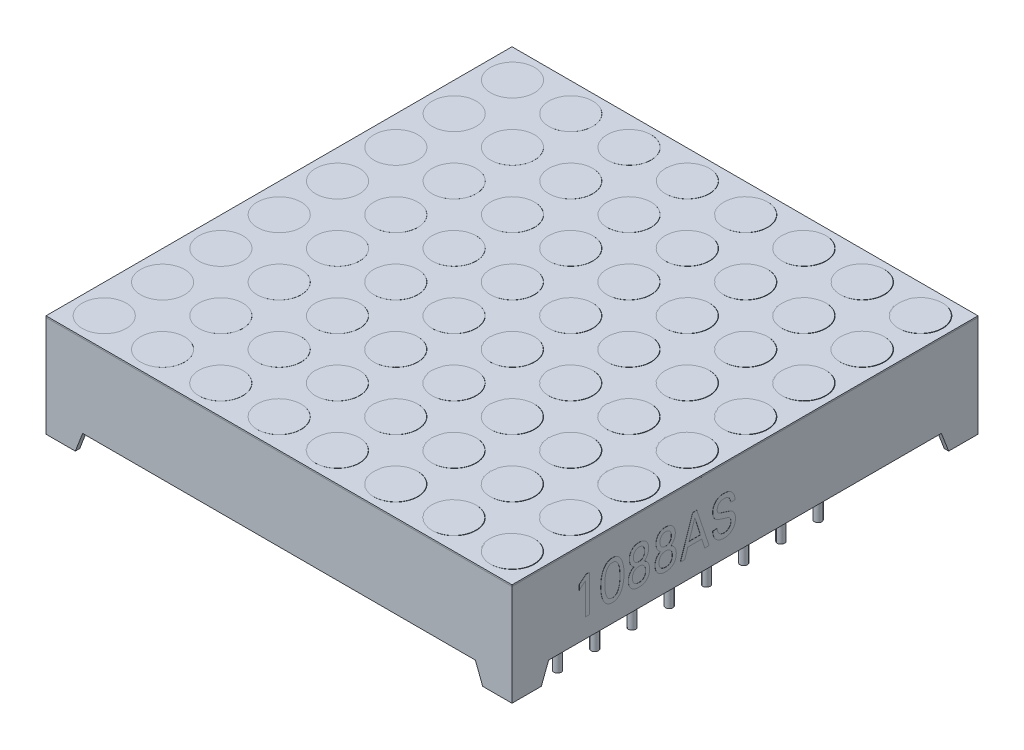
SolidWorks part; units mm, degrees
ref_plane "Front Plane" through (0, 0, 0) normal (0, 0, 1) x (1, 0, 0)
ref_plane "Top Plane" through (0, 0, 0) normal (0, 1, 0) x (1, 0, 0)
ref_plane "Right Plane" through (0, 0, 0) normal (1, 0, 0) x (0, 0, -1)
sketch "Sketch1" plane through (0, 0, 0) normal (0, 1, 0) x (1, 0, 0)
  line L0 (3.975, 31.8) -> (3.975, 0) construction
  line L1 (0, 0) -> (31.8, 0)
  line L2 (0, 0) -> (0, 31.8)
  line L3 (0, 31.8) -> (31.8, 31.8)
  line L4 (31.8, 0) -> (31.8, 31.8)
  line L5 (7.955, 31.8) -> (7.955, 0) construction
  line L6 (11.935, 31.8) -> (11.935, 0) construction
  line L7 (15.915, 31.8) -> (15.915, 0) construction
  line L8 (19.895, 31.8) -> (19.895, 0) construction
  line L9 (23.875, 31.8) -> (23.875, 0) construction
  line L10 (27.855, 31.8) -> (27.855, 0) construction
  line L11 (0, 3.975) -> (31.8, 3.975) construction
  line L12 (0, 7.955) -> (31.8, 7.955) construction
  line L13 (0, 11.935) -> (31.8, 11.935) construction
  line L14 (0, 15.915) -> (31.8, 15.915) construction
  line L15 (0, 19.895) -> (31.8, 19.895) construction
  line L16 (0, 23.875) -> (31.8, 23.875) construction
  line L17 (0, 27.855) -> (31.8, 27.855) construction
  line L18 (0, 0) -> (3.975, 3.975) construction
  line L19 (0, 3.975) -> (3.975, 0) construction
  circle A0 centre (1.9875, 1.9875) radius 1.5
  circle A1 centre (5.9675, 1.9875) radius 1.5
  circle A2 centre (9.9475, 1.9875) radius 1.5
  circle A3 centre (13.9275, 1.9875) radius 1.5
  circle A4 centre (17.9075, 1.9875) radius 1.5
  circle A5 centre (21.8875, 1.9875) radius 1.5
  circle A6 centre (25.8675, 1.9875) radius 1.5
  circle A7 centre (29.8475, 1.9875) radius 1.5
  circle A8 centre (5.9675, 5.9675) radius 1.5
  circle A9 centre (9.9475, 5.9675) radius 1.5
  circle A10 centre (13.9275, 5.9675) radius 1.5
  circle A11 centre (17.9075, 5.9675) radius 1.5
  circle A12 centre (21.8875, 5.9675) radius 1.5
  circle A13 centre (25.8675, 5.9675) radius 1.5
  circle A14 centre (29.8475, 5.9675) radius 1.5
  circle A15 centre (5.9675, 9.9475) radius 1.5
  circle A16 centre (9.9475, 9.9475) radius 1.5
  circle A17 centre (13.9275, 9.9475) radius 1.5
  circle A18 centre (17.9075, 9.9475) radius 1.5
  circle A19 centre (21.8875, 9.9475) radius 1.5
  circle A20 centre (25.8675, 9.9475) radius 1.5
  circle A21 centre (29.8475, 9.9475) radius 1.5
  circle A22 centre (5.9675, 13.9275) radius 1.5
  circle A23 centre (9.9475, 13.9275) radius 1.5
  circle A24 centre (13.9275, 13.9275) radius 1.5
  circle A25 centre (17.9075, 13.9275) radius 1.5
  circle A26 centre (21.8875, 13.9275) radius 1.5
  circle A27 centre (25.8675, 13.9275) radius 1.5
  circle A28 centre (29.8475, 13.9275) radius 1.5
  circle A29 centre (5.9675, 17.9075) radius 1.5
  circle A30 centre (9.9475, 17.9075) radius 1.5
  circle A31 centre (13.9275, 17.9075) radius 1.5
  circle A32 centre (17.9075, 17.9075) radius 1.5
  circle A33 centre (21.8875, 17.9075) radius 1.5
  circle A34 centre (25.8675, 17.9075) radius 1.5
  circle A35 centre (29.8475, 17.9075) radius 1.5
  circle A36 centre (5.9675, 21.8875) radius 1.5
  circle A37 centre (9.9475, 21.8875) radius 1.5
  circle A38 centre (13.9275, 21.8875) radius 1.5
  circle A39 centre (17.9075, 21.8875) radius 1.5
  circle A40 centre (21.8875, 21.8875) radius 1.5
  circle A41 centre (25.8675, 21.8875) radius 1.5
  circle A42 centre (29.8475, 21.8875) radius 1.5
  circle A43 centre (5.9675, 25.8675) radius 1.5
  circle A44 centre (9.9475, 25.8675) radius 1.5
  circle A45 centre (13.9275, 25.8675) radius 1.5
  circle A46 centre (17.9075, 25.8675) radius 1.5
  circle A47 centre (21.8875, 25.8675) radius 1.5
  circle A48 centre (25.8675, 25.8675) radius 1.5
  circle A49 centre (29.8475, 25.8675) radius 1.5
  circle A50 centre (5.9675, 29.8475) radius 1.5
  circle A51 centre (9.9475, 29.8475) radius 1.5
  circle A52 centre (13.9275, 29.8475) radius 1.5
  circle A53 centre (17.9075, 29.8475) radius 1.5
  circle A54 centre (21.8875, 29.8475) radius 1.5
  circle A55 centre (25.8675, 29.8475) radius 1.5
  circle A56 centre (29.8475, 29.8475) radius 1.5
  circle A57 centre (1.9875, 5.9675) radius 1.5
  circle A58 centre (1.9875, 9.9475) radius 1.5
  circle A59 centre (1.9875, 13.9275) radius 1.5
  circle A60 centre (1.9875, 17.9075) radius 1.5
  circle A61 centre (1.9875, 21.8875) radius 1.5
  circle A62 centre (1.9875, 25.8675) radius 1.5
  circle A63 centre (1.9875, 29.8475) radius 1.5
  dimension "D7" = 8
  dimension "D1" = 31.8
  dimension "D2" = 31.8
  dimension "D3" = 3.975
  dimension "D5" = 3.975
  dimension "D4" = 7
  dimension "D6" = 7
  dimension "D8" = 8
extrude "TOP MASK" add sketch "Sketch1" against normal blind 0.1
sketch "Sketch2" plane through (0, -0.1, 0) normal (0, -1, 0) x (1, 0, 0)
  line L0 (31.8, 0) -> (31.8, -31.8) construction
  line L1 (31.8, -31.8) -> (0, -31.8) construction
  line L2 (0, -31.8) -> (0, 0) construction
  line L3 (0, 0) -> (31.8, 0) construction
  line L4 (31.8, 0) -> (31.8, -31.8)
  line L5 (31.8, -31.8) -> (0, -31.8)
  line L6 (0, -31.8) -> (0, 0)
  line L7 (0, 0) -> (31.8, 0)
  line L8 (31.5, -0.3) -> (31.5, -31.5)
  line L9 (31.5, -31.5) -> (0.3, -31.5)
  line L10 (0.3, -31.5) -> (0.3, -0.3)
  line L11 (0.3, -0.3) -> (31.5, -0.3)
  dimension "D1" = 0.3
extrude "SIDES" add sketch "Sketch2" along normal blind 6.9 separate body
sketch "Sketch3" plane through (0, 0, -31.8) normal (0, 0, -1) x (-1, 0, 0)
  line L0 (-2, -7) -> (-29.8, -7)
  line L2 (-2, -7) -> (-2.5, -5.7)
  line L3 (-29.8, -7) -> (-29.8035, -7.0031)
  line L8 (-29.8, -7) -> (-29.3, -5.7)
  line L9 (-29.3, -5.7) -> (-2.5, -5.7)
  line M7 (-31.8, -7) -> (0, -7)
extrude "Cut-Extrude2" cut sketch "Sketch3" against normal through all both and the other way through all contours L9 L8 L2 M7
sketch "Sketch4" plane through (0, 0, 0) normal (-1, 0, 0) x (0, 0, 1)
  line L0 (-29.8, -7) -> (-29.3, -5.7)
  line L1 (0, -7) -> (-31.8, -7) construction
  line L2 (-29.3, -5.7) -> (-2.5, -5.7)
  line L3 (-2.5, -5.7) -> (-2, -7)
  line L4 (-2, -7) -> (-29.8, -7)
  line L5 (-31.8, -7) -> (-31.8, -0.1) construction
  line L6 (0, -7) -> (0, -0.1) construction
  line L7 (0, -5.7) -> (-0.3, -5.7) construction
  dimension "D1" = 2
  dimension "D2" = 2.5
  dimension "D3" = 2
  dimension "D4" = 2.5
extrude "Cut-Extrude3" cut sketch "Sketch4" against normal through all
sketch "Sketch5" plane through (0, 0, 0) normal (0, 1, 0) x (1, 0, 0)
  circle A0 centre (1.9875, 1.9875) radius 1.5 construction
  circle A1 centre (1.9875, 1.9875) radius 1.5
  circle A2 centre (5.9625, 1.9875) radius 1.5
  circle A3 centre (9.9375, 1.9875) radius 1.5
  circle A4 centre (13.9125, 1.9875) radius 1.5
  circle A5 centre (17.8875, 1.9875) radius 1.5
  circle A6 centre (21.8625, 1.9875) radius 1.5
  circle A7 centre (25.8375, 1.9875) radius 1.5
  circle A8 centre (29.8125, 1.9875) radius 1.5
  circle A9 centre (5.9625, 5.9675) radius 1.5
  circle A10 centre (9.9375, 5.9675) radius 1.5
  circle A11 centre (13.9125, 5.9675) radius 1.5
  circle A12 centre (17.8875, 5.9675) radius 1.5
  circle A13 centre (21.8625, 5.9675) radius 1.5
  circle A14 centre (25.8375, 5.9675) radius 1.5
  circle A15 centre (29.8125, 5.9675) radius 1.5
  circle A16 centre (5.9625, 9.9475) radius 1.5
  circle A17 centre (9.9375, 9.9475) radius 1.5
  circle A18 centre (13.9125, 9.9475) radius 1.5
  circle A19 centre (17.8875, 9.9475) radius 1.5
  circle A20 centre (21.8625, 9.9475) radius 1.5
  circle A21 centre (25.8375, 9.9475) radius 1.5
  circle A22 centre (29.8125, 9.9475) radius 1.5
  circle A23 centre (5.9625, 13.9275) radius 1.5
  circle A24 centre (9.9375, 13.9275) radius 1.5
  circle A25 centre (13.9125, 13.9275) radius 1.5
  circle A26 centre (17.8875, 13.9275) radius 1.5
  circle A27 centre (21.8625, 13.9275) radius 1.5
  circle A28 centre (25.8375, 13.9275) radius 1.5
  circle A29 centre (29.8125, 13.9275) radius 1.5
  circle A30 centre (5.9625, 17.9075) radius 1.5
  circle A31 centre (9.9375, 17.9075) radius 1.5
  circle A32 centre (13.9125, 17.9075) radius 1.5
  circle A33 centre (17.8875, 17.9075) radius 1.5
  circle A34 centre (21.8625, 17.9075) radius 1.5
  circle A35 centre (25.8375, 17.9075) radius 1.5
  circle A36 centre (29.8125, 17.9075) radius 1.5
  circle A37 centre (5.9625, 21.8875) radius 1.5
  circle A38 centre (9.9375, 21.8875) radius 1.5
  circle A39 centre (13.9125, 21.8875) radius 1.5
  circle A40 centre (17.8875, 21.8875) radius 1.5
  circle A41 centre (21.8625, 21.8875) radius 1.5
  circle A42 centre (25.8375, 21.8875) radius 1.5
  circle A43 centre (29.8125, 21.8875) radius 1.5
  circle A44 centre (5.9625, 25.8675) radius 1.5
  circle A45 centre (9.9375, 25.8675) radius 1.5
  circle A46 centre (13.9125, 25.8675) radius 1.5
  circle A47 centre (17.8875, 25.8675) radius 1.5
  circle A48 centre (21.8625, 25.8675) radius 1.5
  circle A49 centre (25.8375, 25.8675) radius 1.5
  circle A50 centre (29.8125, 25.8675) radius 1.5
  circle A51 centre (5.9625, 29.8475) radius 1.5
  circle A52 centre (9.9375, 29.8475) radius 1.5
  circle A53 centre (13.9125, 29.8475) radius 1.5
  circle A54 centre (17.8875, 29.8475) radius 1.5
  circle A55 centre (21.8625, 29.8475) radius 1.5
  circle A56 centre (25.8375, 29.8475) radius 1.5
  circle A57 centre (29.8125, 29.8475) radius 1.5
  circle A58 centre (1.9875, 5.9675) radius 1.5
  circle A59 centre (1.9875, 9.9475) radius 1.5
  circle A60 centre (1.9875, 13.9275) radius 1.5
  circle A61 centre (1.9875, 17.9075) radius 1.5
  circle A62 centre (1.9875, 21.8875) radius 1.5
  circle A63 centre (1.9875, 25.8675) radius 1.5
  circle A64 centre (1.9875, 29.8475) radius 1.5
  dimension "D1" = 8
  dimension "D2" = 8
extrude "Boss-Extrude3" add sketch "Sketch5" against normal blind 0.1 separate body
sketch "Sketch6" plane through (0, -5.7, 0) normal (0, -1, 0) x (1, 0, 0)
  line L1 (0.3, -0.3) -> (31.5, -0.3)
  line L2 (0.3, -0.3) -> (0.3, -31.5)
  line L3 (0.3, -31.5) -> (31.5, -31.5)
  line L4 (31.5, -0.3) -> (31.5, -31.5)
extrude "Boss-Extrude4" add sketch "Sketch6" against normal up to surface (4.1 mm away) from offset 1.5 separate body up to face at (1.9875, -0.1, -28.3475) offset against normal yes
sketch "Sketch7" plane through (0, -4.2, 0) normal (0, -1, 0) x (1, 0, 0)
  line L0 (15.9, 0) -> (15.9, -31.8) construction
  line L1 (29.3, 0) -> (2.5, 0) construction
  line L2 (2.5, -31.8) -> (29.3, -31.8) construction
  line L3 (0, -15.9) -> (31.8, -15.9) construction
  line L4 (0, -2.5) -> (0, -29.3) construction
  line L5 (31.8, -2.5) -> (31.8, -29.3) construction
  circle A0 centre (3.9, -14.63) radius 0.25
  circle A1 centre (3.9, -12.09) radius 0.25
  circle A2 centre (3.9, -9.55) radius 0.25
  circle A3 centre (3.9, -7.01) radius 0.25
  circle A4 centre (27.9, -7.01) radius 0.25
  circle A5 centre (27.9, -9.55) radius 0.25
  circle A6 centre (27.9, -12.09) radius 0.25
  circle A7 centre (27.9, -14.63) radius 0.25
  circle A8 centre (27.9, -17.17) radius 0.25
  circle A9 centre (27.9, -19.71) radius 0.25
  circle A10 centre (27.9, -22.25) radius 0.25
  circle A11 centre (27.9, -24.79) radius 0.25
  circle A12 centre (3.9, -24.79) radius 0.25
  circle A13 centre (3.9, -22.25) radius 0.25
  circle A14 centre (3.9, -19.71) radius 0.25
  circle A15 centre (3.9, -17.17) radius 0.25
  dimension "D1" = 0.5
  dimension "D2" = 1.27
  dimension "D3" = 12
  dimension "D4" = 4
extrude "Boss-Extrude5" add sketch "Sketch7" along normal blind 6.3 from surface at 0 separate body starting at face at (15.9, -4.2, -15.9)
sketch "Sketch8" plane through (31.8, 0, 0) normal (1, 0, 0) x (0, 0, -1)
  text T0 "1088AS" font "@Adobe Heiti Std R" height 2.5
extrude "1088AS" add sketch "Sketch8" along normal blind 0.01 separate body
